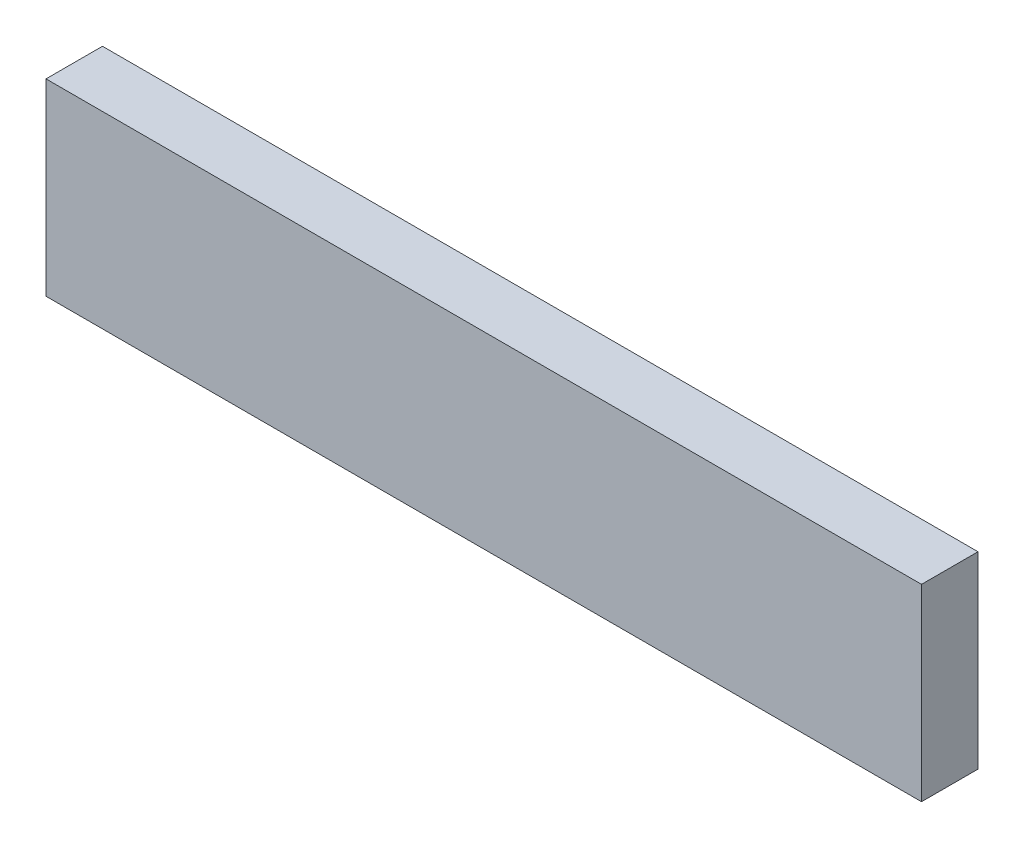
SolidWorks part; units mm, degrees
material "Cedar"
ref_plane "Front Plane" through (0, 0, 0) normal (0, 0, 1) x (1, 0, 0)
ref_plane "Top Plane" through (0, 0, 0) normal (0, 1, 0) x (1, 0, 0)
ref_plane "Right Plane" through (0, 0, 0) normal (1, 0, 0) x (0, 0, -1)
sketch "Sketch1" plane through (0, 0, 0) normal (1, 0, 0) x (0, 0, -1)
  line L1 (-9.525, -31.75) -> (9.525, -31.75)
  line L2 (-9.525, -31.75) -> (-9.525, 31.75)
  line L3 (-9.525, 31.75) -> (9.525, 31.75)
  line L4 (9.525, -31.75) -> (9.525, 31.75)
  line L5 (-9.525, -31.75) -> (9.525, 31.75) construction
  line L6 (-9.525, 31.75) -> (9.525, -31.75) construction
  point P0 (0, 0)
  dimension "D1" = 63.5
  dimension "D2" = 19.05
extrude "Boss-Extrude1" add sketch "Sketch1" along normal blind 295.275
